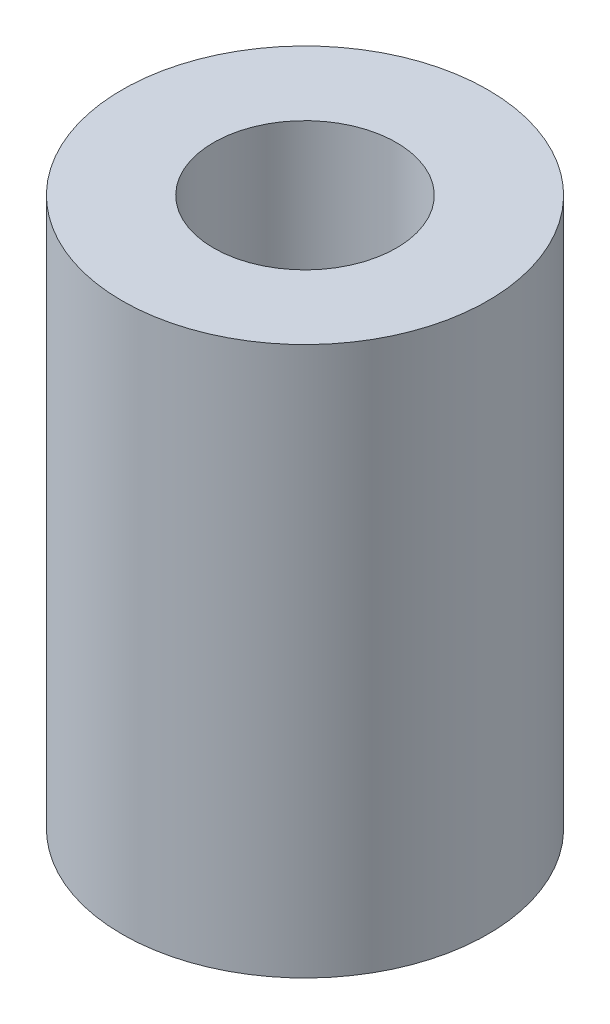
SolidWorks part; units mm, degrees
material "3.0205 (EN-AW 1200)"
ref_plane "Alzado" through (0, 0, 0) normal (0, 0, 1) x (1, 0, 0)
ref_plane "Planta" through (0, 0, 0) normal (0, 1, 0) x (1, 0, 0)
ref_plane "Vista lateral" through (0, 0, 0) normal (1, 0, 0) x (0, 0, -1)
sketch "Croquis1" plane through (0, 0, 0) normal (0, 1, 0) x (1, 0, 0)
  circle A0 centre (0, 0) radius 3
  dimension "D1" = 6
extrude "Saliente-Extruir1" add sketch "Croquis1" along normal blind 9
sketch "Croquis2" plane through (0, 9, 0) normal (0, 1, 0) x (1, 0, 0)
  circle A0 centre (0, 0) radius 1.5
  dimension "D1" = 3
extrude "Cortar-Extruir1" cut sketch "Croquis2" against normal blind 9
